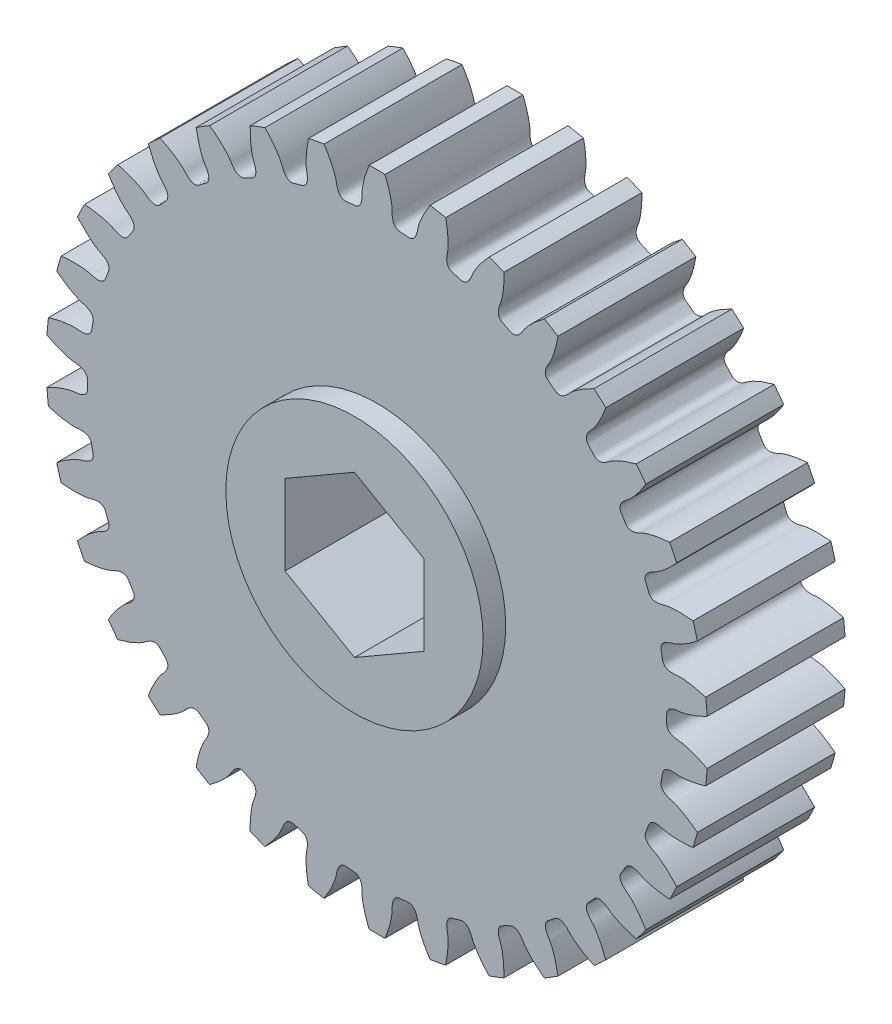
SolidWorks part; units mm, degrees
material "7075-T6 (SN)"
ref_plane "Front Plane" through (0, 0, 0) normal (0, 0, 1) x (1, 0, 0)
ref_plane "Top Plane" through (0, 0, 0) normal (0, 1, 0) x (1, 0, 0)
ref_plane "Right Plane" through (0, 0, 0) normal (1, 0, 0) x (0, 0, -1)
ref_plane "Plane1" through (0, 0, 4.7625) normal (0, 0, 1) x (1, 0, 0)
sketch "Sketch1" plane through (0, 0, 4.7625) normal (0, 0, 1) x (1, 0, 0)
  arc A0 (22.1313, 5.7259) -> (21.8307, 6.7824) centre (0, 0) ccw
  arc A1 (20.7023, 9.695) -> (20.2127, 10.6783) centre (0, 0) ccw
  arc A2 (18.5684, 13.334) -> (17.9064, 14.2105) centre (0, 0) ccw
  arc A3 (15.8021, 16.5189) -> (14.9904, 17.2589) centre (0, 0) ccw
  arc A4 (12.4977, 19.1412) -> (11.5638, 19.7195) centre (0, 0) ccw
  arc A5 (8.7677, 21.1118) -> (7.7435, 21.5086) centre (0, 0) ccw
  arc A6 (4.7392, 22.3634) -> (3.6595, 22.5652) centre (0, 0) ccw
  arc A7 (0.5492, 22.8534) -> (-0.5492, 22.8534) centre (0, 0) ccw
  arc A8 (-3.6595, 22.5652) -> (-4.7392, 22.3634) centre (0, 0) ccw
  arc A9 (-7.7435, 21.5086) -> (-8.7677, 21.1118) centre (0, 0) ccw
  arc A10 (-11.5638, 19.7195) -> (-12.4977, 19.1412) centre (0, 0) ccw
  arc A11 (-14.9904, 17.2589) -> (-15.8021, 16.5189) centre (0, 0) ccw
  arc A12 (-17.9064, 14.2105) -> (-18.5684, 13.334) centre (0, 0) ccw
  arc A13 (-20.2127, 10.6783) -> (-20.7023, 9.695) centre (0, 0) ccw
  arc A14 (-21.8307, 6.7824) -> (-22.1313, 5.7259) centre (0, 0) ccw
  arc A15 (-22.7052, 2.6555) -> (-22.8066, 1.5618) centre (0, 0) ccw
  arc A16 (-22.8066, -1.5618) -> (-22.7052, -2.6555) centre (0, 0) ccw
  arc A17 (-22.1313, -5.7259) -> (-21.8307, -6.7824) centre (0, 0) ccw
  arc A18 (-20.7023, -9.695) -> (-20.2127, -10.6783) centre (0, 0) ccw
  arc A19 (-18.5684, -13.334) -> (-17.9064, -14.2105) centre (0, 0) ccw
  arc A20 (-15.8021, -16.5189) -> (-14.9904, -17.2589) centre (0, 0) ccw
  arc A21 (-12.4977, -19.1412) -> (-11.5638, -19.7195) centre (0, 0) ccw
  arc A22 (-8.7677, -21.1118) -> (-7.7435, -21.5086) centre (0, 0) ccw
  arc A23 (-4.7392, -22.3634) -> (-3.6595, -22.5652) centre (0, 0) ccw
  arc A24 (-0.5492, -22.8534) -> (0.5492, -22.8534) centre (0, 0) ccw
  arc A25 (3.6595, -22.5652) -> (4.7392, -22.3634) centre (0, 0) ccw
  arc A26 (7.7435, -21.5086) -> (8.7677, -21.1118) centre (0, 0) ccw
  arc A27 (11.5638, -19.7195) -> (12.4977, -19.1412) centre (0, 0) ccw
  arc A28 (14.9904, -17.2589) -> (15.8021, -16.5189) centre (0, 0) ccw
  arc A29 (17.9064, -14.2105) -> (18.5684, -13.334) centre (0, 0) ccw
  arc A30 (20.2127, -10.6783) -> (20.7023, -9.695) centre (0, 0) ccw
  arc A31 (21.8307, -6.7824) -> (22.1313, -5.7259) centre (0, 0) ccw
  arc A32 (22.7052, -2.6555) -> (22.8066, -1.5618) centre (0, 0) ccw
  arc A33 (22.8066, 1.5618) -> (22.7052, 2.6555) centre (0, 0) ccw
  spline S0 degree 3 number of poles 89 (22.7052, 2.6555) -> (22.1313, 5.7259)
  spline S1 degree 3 number of poles 89 (21.8307, 6.7824) -> (20.7023, 9.695)
  spline S2 degree 3 number of poles 89 (20.2127, 10.6783) -> (18.5684, 13.334)
  spline S3 degree 3 number of poles 89 (17.9064, 14.2105) -> (15.8021, 16.5189)
  spline S4 degree 3 number of poles 89 (14.9904, 17.2589) -> (12.4977, 19.1412)
  spline S5 degree 3 number of poles 89 (11.5638, 19.7195) -> (8.7677, 21.1118)
  spline S6 degree 3 number of poles 89 (7.7435, 21.5086) -> (4.7392, 22.3634)
  spline S7 degree 3 number of poles 89 (3.6595, 22.5652) -> (0.5492, 22.8534)
  spline S8 degree 3 number of poles 89 (-0.5492, 22.8534) -> (-3.6595, 22.5652)
  spline S9 degree 3 number of poles 89 (-4.7392, 22.3634) -> (-7.7435, 21.5086)
  spline S10 degree 3 number of poles 89 (-8.7677, 21.1118) -> (-11.5638, 19.7195)
  spline S11 degree 3 number of poles 89 (-12.4977, 19.1412) -> (-14.9904, 17.2589)
  spline S12 degree 3 number of poles 89 (-15.8021, 16.5189) -> (-17.9064, 14.2105)
  spline S13 degree 3 number of poles 89 (-18.5684, 13.334) -> (-20.2127, 10.6783)
  spline S14 degree 3 number of poles 89 (-20.7023, 9.695) -> (-21.8307, 6.7824)
  spline S15 degree 3 number of poles 89 (-22.1313, 5.7259) -> (-22.7052, 2.6555)
  spline S16 degree 3 number of poles 89 (-22.8066, 1.5618) -> (-22.8066, -1.5618)
  spline S17 degree 3 number of poles 89 (-22.7052, -2.6555) -> (-22.1313, -5.7259)
  spline S18 degree 3 number of poles 89 (-21.8307, -6.7824) -> (-20.7023, -9.695)
  spline S19 degree 3 number of poles 89 (-20.2127, -10.6783) -> (-18.5684, -13.334)
  spline S20 degree 3 number of poles 89 (-17.9064, -14.2105) -> (-15.8021, -16.5189)
  spline S21 degree 3 number of poles 89 (-14.9904, -17.2589) -> (-12.4977, -19.1412)
  spline S22 degree 3 number of poles 89 (-11.5638, -19.7195) -> (-8.7677, -21.1118)
  spline S23 degree 3 number of poles 89 (-7.7435, -21.5086) -> (-4.7392, -22.3634)
  spline S24 degree 3 number of poles 89 (-3.6595, -22.5652) -> (-0.5492, -22.8534)
  spline S25 degree 3 number of poles 89 (0.5492, -22.8534) -> (3.6595, -22.5652)
  spline S26 degree 3 number of poles 89 (4.7392, -22.3634) -> (7.7435, -21.5086)
  spline S27 degree 3 number of poles 89 (8.7677, -21.1118) -> (11.5638, -19.7195)
  spline S28 degree 3 number of poles 89 (12.4977, -19.1412) -> (14.9904, -17.2589)
  spline S29 degree 3 number of poles 89 (15.8021, -16.5189) -> (17.9064, -14.2105)
  spline S30 degree 3 number of poles 89 (18.5684, -13.334) -> (20.2127, -10.6783)
  spline S31 degree 3 number of poles 89 (20.7023, -9.695) -> (21.8307, -6.7824)
  spline S32 degree 3 number of poles 89 (22.1313, -5.7259) -> (22.7052, -2.6555)
  spline S33 degree 3 number of poles 89 (22.8066, -1.5618) -> (22.8066, 1.5618)
extrude "Boss-Extrude1" add sketch "Sketch1" against normal blind 9.525
sketch "Sketch2" plane through (0, 0, 4.7625) normal (0, 0, 1) x (1, 0, 0)
  circle A0 centre (0, 0) radius 8.89
extrude "Boss-Extrude2" add sketch "Sketch2" along normal blind 1.5621
sketch "Sketch3" plane through (0, 0, -4.7625) normal (0, 0, -1) x (-1, 0, 0)
  circle A0 centre (0, 0) radius 8.89
extrude "Boss-Extrude3" add sketch "Sketch3" along normal blind 1.5621
sketch "Sketch4" plane through (0, 0, -6.3246) normal (0, 0, -1) x (-1, 0, 0)
  line L0 (-4.8006, -2.7716) -> (0, -5.5433)
  line L1 (0, -5.5433) -> (4.8006, -2.7716)
  line L2 (4.8006, -2.7716) -> (4.8006, 2.7716)
  line L3 (4.8006, 2.7716) -> (0, 5.5433)
  line L4 (0, 5.5433) -> (-4.8006, 2.7716)
  line L5 (-4.8006, 2.7716) -> (-4.8006, -2.7716)
extrude "Cut-Extrude1" cut sketch "Sketch4" against normal through all
